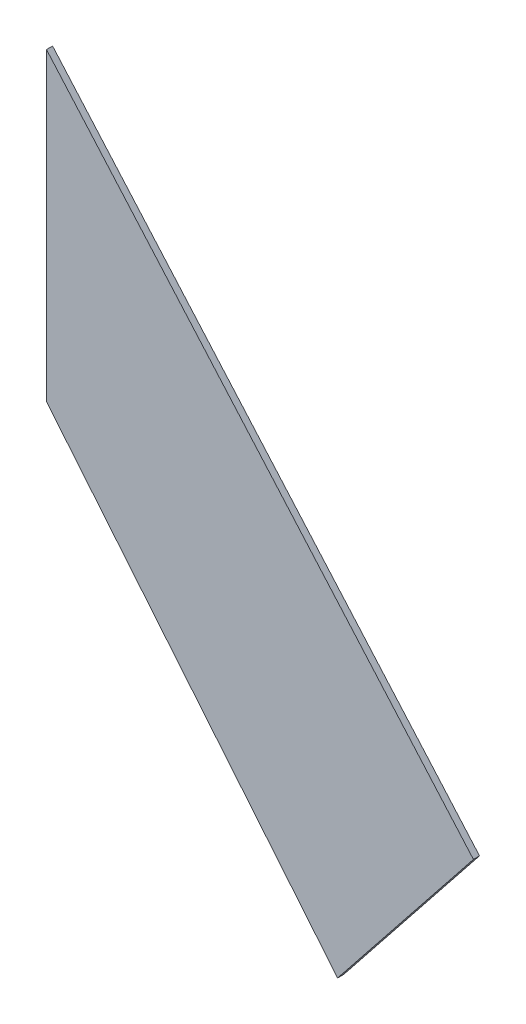
SolidWorks part; units mm, degrees
ref_plane "Alzado" through (0, 0, 0) normal (0, 0, 1) x (1, 0, 0)
ref_plane "Planta" through (0, 0, 0) normal (0, 1, 0) x (1, 0, 0)
ref_plane "Vista lateral" through (0, 0, 0) normal (1, 0, 0) x (0, 0, -1)
sketch "Model" plane through (0, 0, 0) normal (0, 0, 1) x (1, 0, 0)
  line L0 (42.6157, 18.8679) -> (35.6157, 26.8679)
  line L1 (40.3888, 16.0705) -> (42.6157, 18.8679)
  line L2 (35.6157, 21.8679) -> (40.3888, 16.0705)
  line L3 (35.6157, 26.8679) -> (35.6157, 21.8679)
  point P4 (0, 0)
extrude "Saliente-Extruir1" add sketch "Model" along normal blind 0.1
